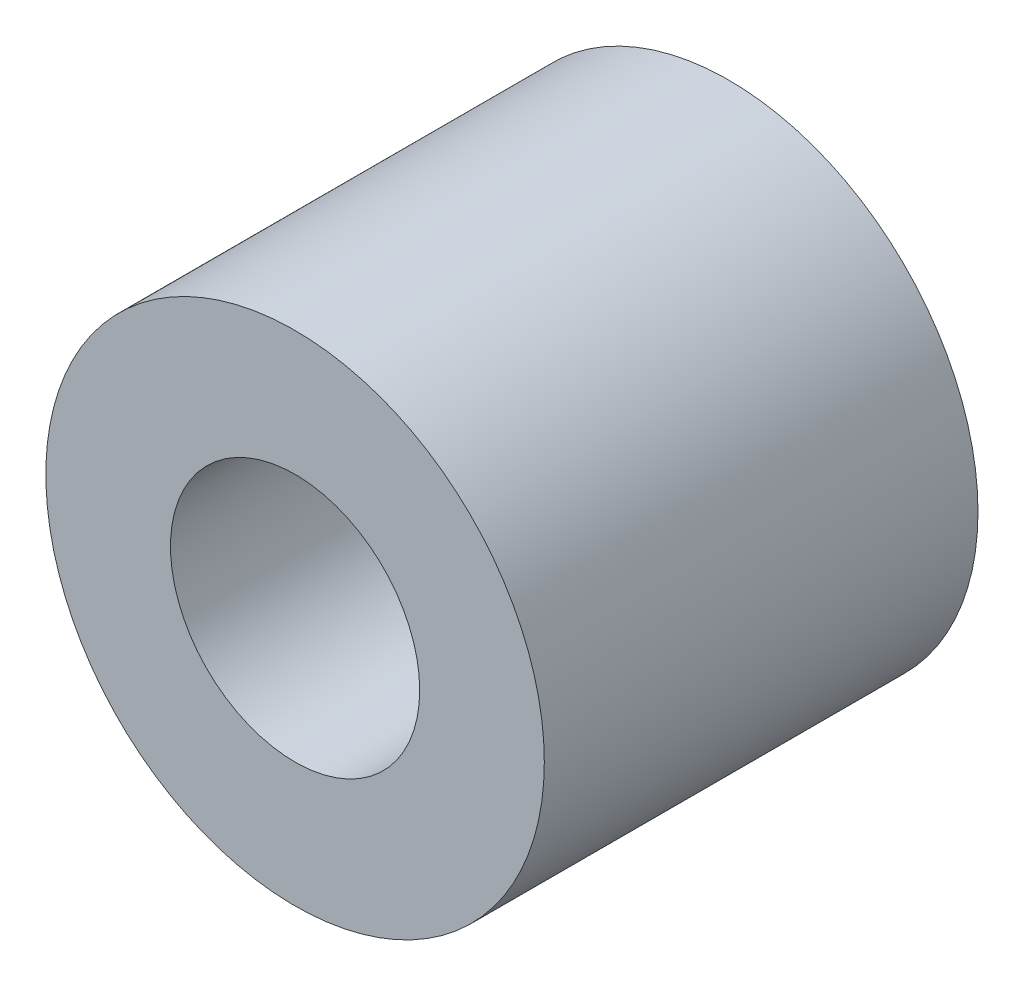
SolidWorks part; units mm, degrees
ref_plane "Front Plane" through (0, 0, 0) normal (0, 0, 1) x (1, 0, 0)
ref_plane "Top Plane" through (0, 0, 0) normal (0, 1, 0) x (1, 0, 0)
ref_plane "Right Plane" through (0, 0, 0) normal (1, 0, 0) x (0, 0, -1)
sketch "Sketch1" plane through (0, 0, 0) normal (0, 0, 1) x (1, 0, 0)
  circle A0 centre (0, 0) radius 5
  dimension "D1" = 10
extrude "Boss-Extrude1" add sketch "Sketch1" along normal blind 8.7
hole_wizard "Ø5.0mm Dowel Hole1" positions "Sketch2" profile "Sketch3" hole size "Ø5.0" standard "ANSI Metric" end condition up to next
sketch "Sketch2" plane through (0, 0, 8.7) normal (0, 0, 1) x (1, 0, 0)
  point P0 (0, 0)
sketch "Sketch3" plane through (0, 0, 8.7) normal (1, 0, 0) x (0, -1, 0)
  line L0 (0, 0) -> (0, 8.7)
  line L1 (0, 8.7) -> (2.5, 8.7)
  line L2 (2.5, 8.7) -> (2.5, 0)
  line L5 (2.5, 0) -> (0, 0)
  line L11 (0, -6.35) -> (0, 107.95) construction
  dimension "Thru Hole Dia." = 5
  dimension "Thru Hole Depth" = 8.7
